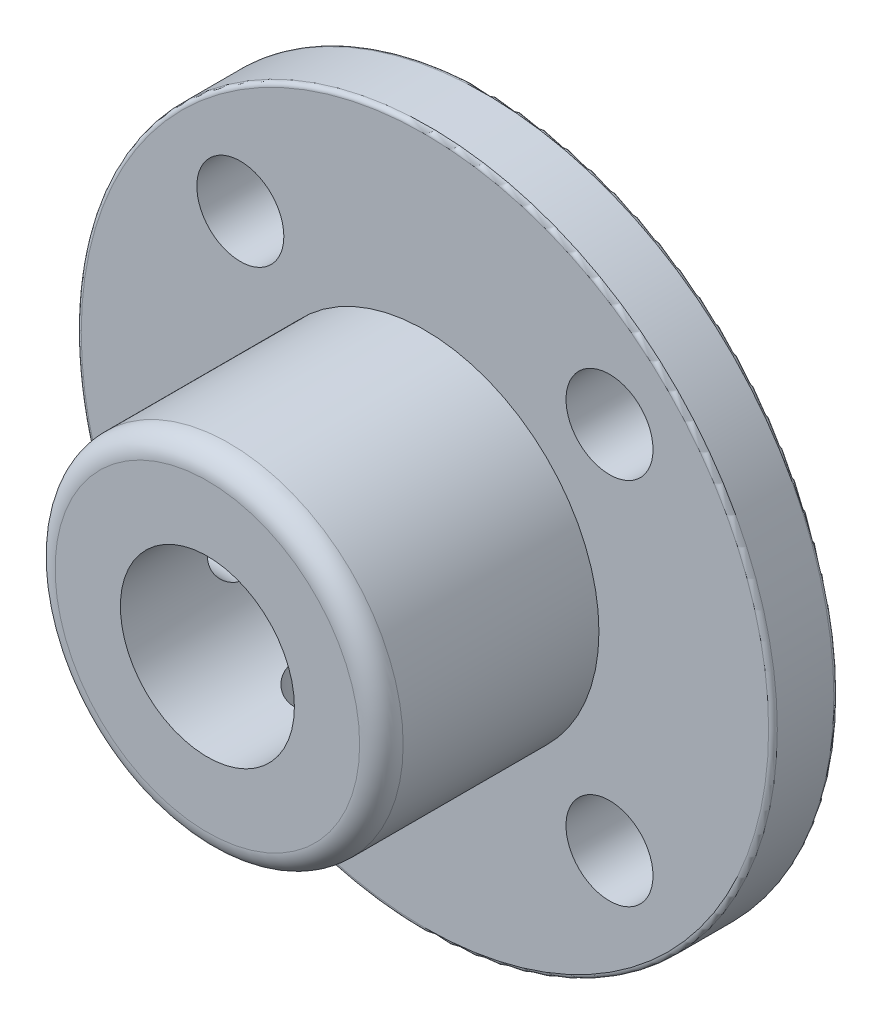
SolidWorks part; units mm, degrees
ref_plane "Front Plane" through (0, 0, 0) normal (0, 0, 1) x (1, 0, 0)
ref_plane "Top Plane" through (0, 0, 0) normal (0, 1, 0) x (1, 0, 0)
ref_plane "Right Plane" through (0, 0, 0) normal (1, 0, 0) x (0, 0, -1)
sketch "Sketch1" plane through (0, 0, 0) normal (0, 0, 1) x (1, 0, 0)
  circle A0 centre (0, 0) radius 16
  dimension "D1" = 32
extrude "Boss-Extrude1" add sketch "Sketch1" along normal blind 3
sketch "Sketch2" plane through (0, 0, 3) normal (0, 0, 1) x (1, 0, 0)
  circle A0 centre (0, 0) radius 8
  dimension "D1" = 16
extrude "Boss-Extrude2" add sketch "Sketch2" along normal blind 10
sketch "Sketch3" plane through (0, 0, 13) normal (0, 0, 1) x (1, 0, 0)
  circle A0 centre (0, 0) radius 4
  dimension "D1" = 8
extrude "Cut-Extrude1" cut sketch "Sketch3" against normal through all
sketch "Sketch4" plane through (0, 0, 3) normal (0, 0, 1) x (1, 0, 0)
  line L1 (-8.4853, -8.4853) -> (8.4853, -8.4853) construction
  line L2 (-8.4853, -8.4853) -> (-8.4853, 8.4853) construction
  line L3 (-8.4853, 8.4853) -> (8.4853, 8.4853) construction
  line L4 (8.4853, -8.4853) -> (8.4853, 8.4853) construction
  line L5 (-8.4853, -8.4853) -> (8.4853, 8.4853) construction
  line L6 (-8.4853, 8.4853) -> (8.4853, -8.4853) construction
  circle A0 centre (-8.4853, 8.4853) radius 2
  circle A1 centre (8.4853, 8.4853) radius 2
  circle A2 centre (8.4853, -8.4853) radius 2
  circle A3 centre (-8.4853, -8.4853) radius 2
  point P0 (0, 0)
  dimension "D2" = 4
  dimension "D1" = 24
extrude "Cut-Extrude2" cut sketch "Sketch4" against normal through all
fillet "Fillet1" radius 1 1 edges at (8, 0, 13)
sketch "Sketch5" plane through (0, 0, 0) normal (1, 0, 0) x (0, 0, -1)
  line L0 (-12, 8) -> (-3, -8) construction
  circle A0 centre (-7.5, 0) radius 1.5
  dimension "D1" = 3
extrude "Cut-Extrude3" cut sketch "Sketch5" against normal blind 9
sketch "Sketch6" plane through (0, 0, 0) normal (0, 1, 0) x (1, 0, 0)
  line L0 (-8, -12) -> (8, -3) construction
  circle A0 centre (0, -7.5) radius 1.5
  dimension "D1" = 3
extrude "Cut-Extrude4" cut sketch "Sketch6" against normal blind 9
fillet "Fillet2" radius 0.2 2 edges at (16, 0, 0) (16, 0, 3)
